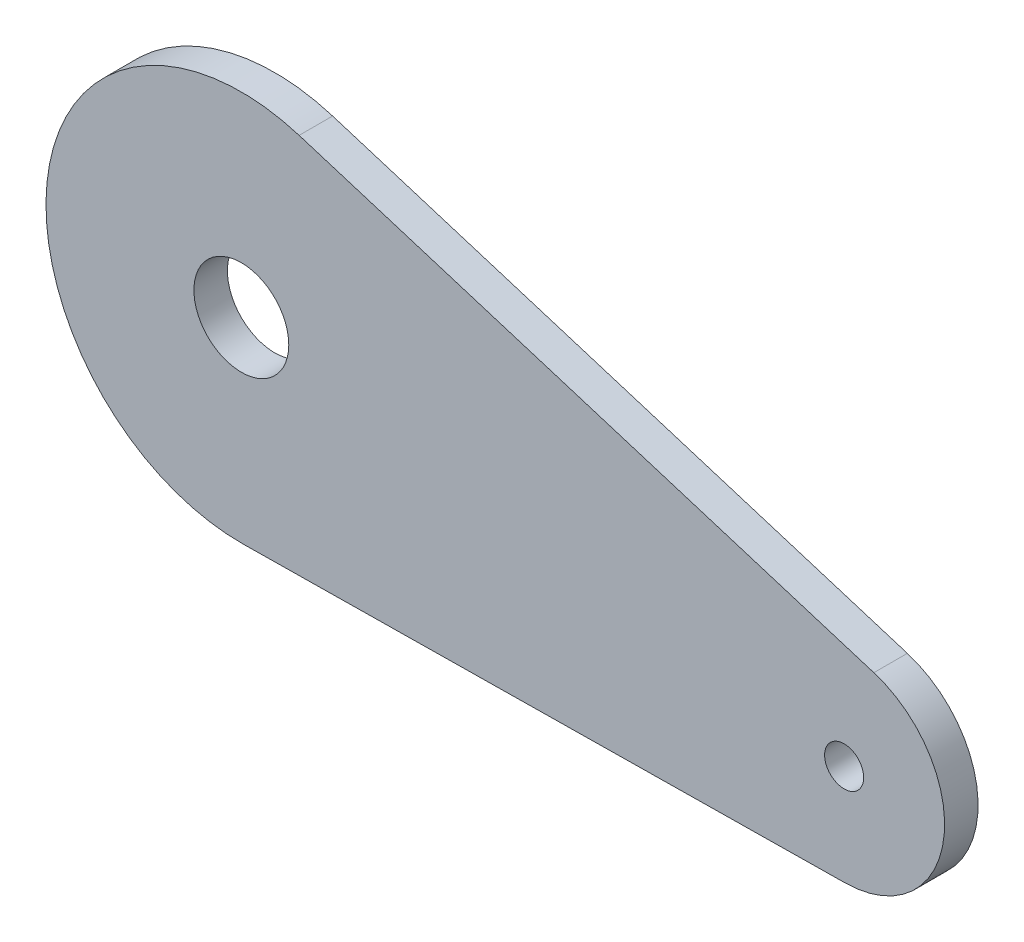
SolidWorks part; units mm, degrees
ref_plane "Płaszczyzna przednia" through (0, 0, 0) normal (0, 0, 1) x (1, 0, 0)
ref_plane "Płaszczyzna górna" through (0, 0, 0) normal (0, 1, 0) x (1, 0, 0)
ref_plane "Płaszczyzna prawa" through (0, 0, 0) normal (1, 0, 0) x (0, 0, -1)
sketch "Szkic1" plane through (0, 0, 0) normal (0, 0, 1) x (1, 0, 0)
  line L0 (-20.22, 57.58) -> (33.78, 49.7571) construction
  line L1 (-20.22, 57.58) -> (33.78, 49.7571) construction
  line L2 (-15.0436, 74.2969) -> (36.4421, 58.3544)
  line L3 (33.893, 40.7578) -> (-20.0004, 40.0814)
  circle A0 centre (-20.22, 57.58) radius 17.5 construction
  circle A1 centre (-20.22, 57.58) radius 17.5 construction
  circle A2 centre (33.78, 49.7571) radius 9 construction
  arc A3 (-20.0004, 40.0814) -> (-15.0436, 74.2969) centre (-20.22, 57.58) cw
  arc A4 (36.4421, 58.3544) -> (33.893, 40.7578) centre (33.78, 49.7571) cw
  circle A5 centre (-20.22, 57.58) radius 4.25
  circle A6 centre (33.78, 49.7571) radius 1.75
  dimension "D1" = 18
  dimension "D2" = 3.5
  dimension "D3" = 8.5
extrude "Dodanie-wyciągnięcie1" add sketch "Szkic1" along normal blind 3
